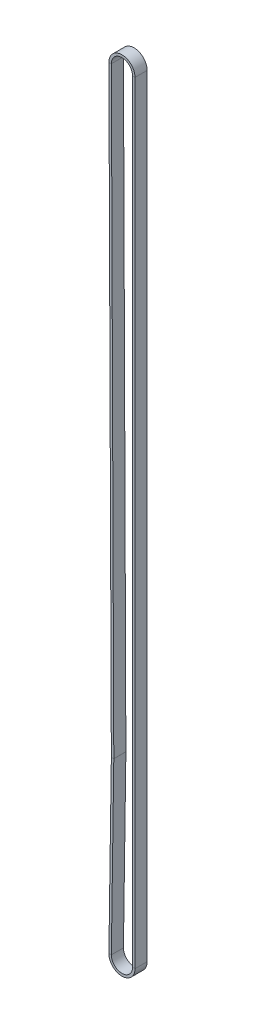
SolidWorks part; units mm, degrees
ref_plane "Front Plane" through (0, 0, 0) normal (0, 0, 1) x (1, 0, 0)
ref_plane "Top Plane" through (0, 0, 0) normal (0, 1, 0) x (1, 0, 0)
ref_plane "Right Plane" through (0, 0, 0) normal (1, 0, 0) x (0, 0, -1)
sketch "Sketch2" plane through (0, 0, 0) normal (0, 0, 1) x (1, 0, 0)
  line L0 (0, 0) -> (1, 0) construction
  line L1 (0, 0) -> (0, 1) construction
  line L2 (7.2181, -470.662) -> (7.2181, 0)
  line L4 (-7.218, -0.0294) -> (-5.727, -366.2382)
  line L5 (-5.7273, -366.287) -> (-7.2173, -470.5589)
  arc A0 (-7.2173, -470.5589) -> (7.2181, -470.662) centre (0, -470.662) ccw
  arc A1 (7.2181, 0) -> (-7.218, -0.0294) centre (0, 0) ccw
  arc A2 (-5.727, -366.2382) -> (-5.7273, -366.287) centre (-8.382, -366.249) cw
sketch "Sketch3" plane through (0, 0, 0) normal (0, 1, 0) x (1, 0, 0)
  line L0 (-6.4681, 0) -> (0, 0)
  line L1 (-6.4681, 0) -> (-7.9681, 0)
  line L2 (-6.4681, 0) -> (-6.4681, -7.366)
  line L3 (-6.4681, -7.366) -> (-7.9681, -7.366)
  line L4 (-7.9681, 0) -> (-7.9681, -7.366)
  dimension "D1" = 1.5
  dimension "D2" = 7.366
  dimension "D3" = 6.4681
sweep "Sweep2" add profiles "Sketch3" path "Sketch2"
